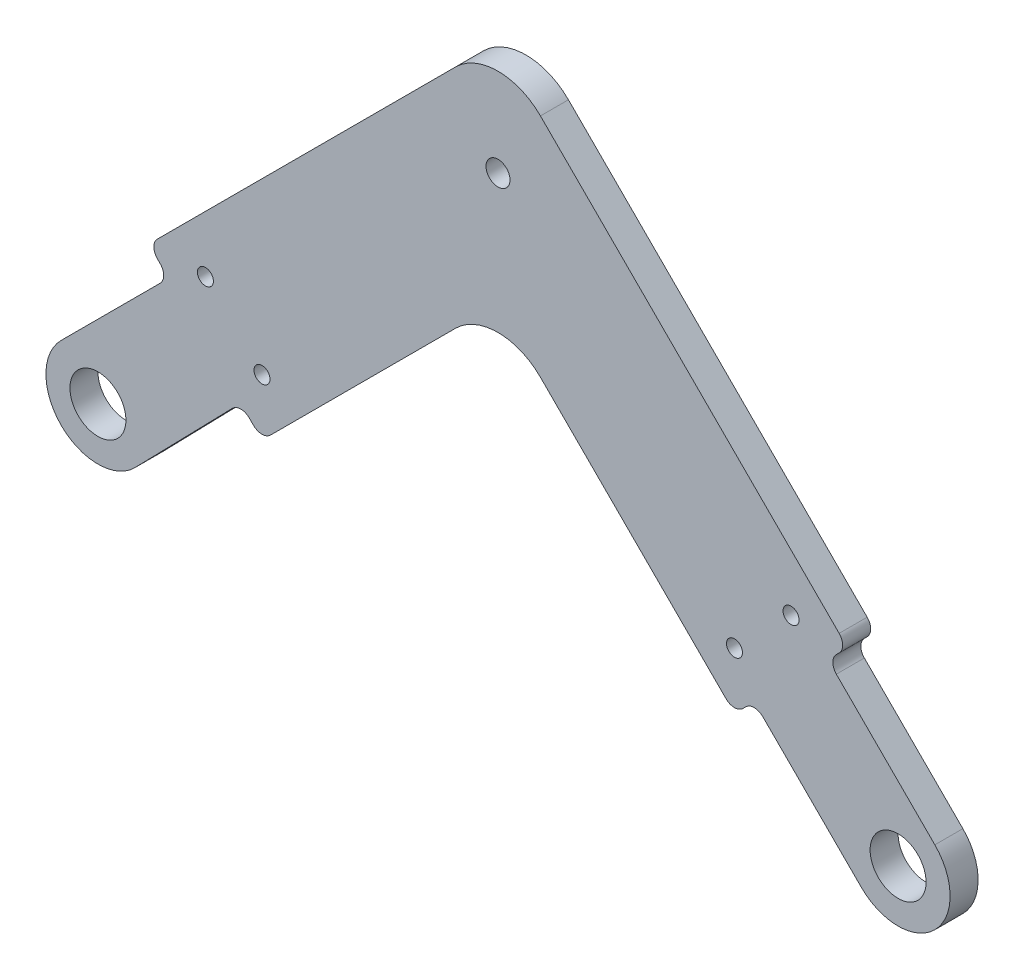
SolidWorks part; units mm, degrees
ref_plane "Front Plane" through (0, 0, 0) normal (0, 0, 1) x (1, 0, 0)
ref_plane "Top Plane" through (0, 0, 0) normal (0, 1, 0) x (1, 0, 0)
ref_plane "Right Plane" through (0, 0, 0) normal (1, 0, 0) x (0, 0, -1)
sketch "Sketch1" plane through (0, 0, 0) normal (0, 0, 1) x (1, 0, 0)
  line L0 (-100, 0) -> (100, 0) construction
  line L1 (0, 0) -> (0, 75.9094) construction
  line L2 (-40, 60) -> (40, 60) construction
  line L4 (0, 99.9354) -> (0, 75.9094) construction
  line L6 (0, 0) -> (-50, 50) construction
  line L7 (-100, 0) -> (0, 100) construction
  line L8 (0, 100) -> (100, 0) construction
  circle A0 centre (-100, 0) radius 20
  circle A1 centre (0, 0) radius 20
  circle A2 centre (100, 0) radius 20
  dimension "D4" = 40
  dimension "D1" = 200
  dimension "D2" = 100
  dimension "D3" = 80
sketch "Sketch3" plane through (0, 0, 0) normal (0, 0, 1) x (1, 0, 0)
  line L0 (-40, 60) -> (-56.5165, 43.4835) construction
  line L1 (81.9688, 8.8388) -> (95.4038, -4.5962)
  line L2 (-40, 60) -> (40, 60) construction
  line L3 (40, 60) -> (86.565, 13.435) construction
  line L4 (0, 100) -> (100, 0) construction
  line L5 (-100, 0) -> (0, 100) construction
  line L6 (44.1421, 70) -> (93.636, 20.5061)
  line L7 (-44.1421, 70) -> (44.1421, 70)
  line L8 (-44.1421, 70) -> (-63.5876, 50.5546)
  line L9 (35.8579, 50) -> (79.4939, 6.364)
  line L10 (-35.8579, 50) -> (35.8579, 50)
  line L11 (-35.8579, 50) -> (-49.4454, 36.4124)
  line L12 (-63.5876, 50.5546) -> (-49.4454, 36.4124)
  line L13 (79.4939, 6.364) -> (93.636, 20.5061)
  line L14 (104.5962, 4.5962) -> (91.1612, 18.0312)
  line L15 (0, 99.9354) -> (0, 75.9094) construction
  line L16 (-3.4532, 85.4203) -> (-6, 70)
  line L17 (3.4532, 85.4203) -> (6, 70)
  line L19 (0, 0) -> (0, 75.9094) construction
  line L20 (75.9584, 9.8995) -> (90.1005, 24.0416) construction
  circle A0 centre (100, 0) radius 10 construction
  circle A1 centre (100, 0) radius 3.5
  arc A2 (95.4038, -4.5962) -> (104.5962, 4.5962) centre (100, 0) ccw
  circle A3 centre (0, 60) radius 1.5
  circle A4 centre (0, 84.85) radius 1.5
  arc A5 (3.4532, 85.4203) -> (-3.4532, 85.4203) centre (0, 84.85) ccw
  circle A6 centre (79.4939, 13.435) radius 1
  circle A7 centre (86.565, 20.5061) radius 1
  circle A8 centre (0, 84.85) radius 3.5 construction
  circle A9 centre (100, 0) radius 6.5 construction
  circle A10 centre (-50, 50) radius 1.5
  dimension "D5" = 20
  dimension "D6" = 7
  dimension "D9" = 3
  dimension "D10" = 3
  dimension "D16" = 2
  dimension "D19" = 3
  dimension "D3" = 27.5
  dimension "D4" = 19
  dimension "D8" = 90
  dimension "D11" = 14.85
  dimension "D12" = 2
  dimension "D13" = 6
  dimension "D14" = 6
  dimension "D15" = 5
  dimension "D17" = 5
  dimension "D18" = 5
  dimension "D1" = 10
  dimension "D2" = 10
  dimension "D7" = 3
sketch "Sketch4" plane through (0, 0, 0) normal (0, 0, 1) x (1, 0, 0)
  line L0 (-86.565, 13.435) -> (-50, 50) construction
  line L1 (-100, 0) -> (0, 100) construction
  line L2 (-50, 50) -> (-13.3744, 13.3744) construction
  line L3 (0, 0) -> (-50, 50) construction
  line L4 (-79.4939, 6.364) -> (-50, 35.8579)
  line L5 (-50, 35.8579) -> (-20.4455, 6.3033)
  line L6 (-93.636, 20.5061) -> (-50, 64.1421)
  line L7 (-50, 64.1421) -> (-6.3033, 20.4455)
  line L8 (-93.636, 20.5061) -> (-79.4939, 6.364)
  line L10 (-82.1491, 9.0191) -> (-95.3424, -4.534)
  line L11 (-91.1612, 18.0312) -> (-104.5962, 4.5962)
  line L12 (-20.4455, 6.3033) -> (-6.3033, 20.4455)
  line L13 (-8.7782, 17.9706) -> (4.5962, 4.5962)
  line L14 (-17.9706, 8.7782) -> (-4.5962, -4.5962)
  line L15 (-90.1005, 24.0416) -> (-75.9584, 9.8995) construction
  line L16 (-23.981, 9.8389) -> (-9.8389, 23.981) construction
  circle A0 centre (-100, 0) radius 10 construction
  circle A1 centre (-100, 0) radius 3.5
  circle A2 centre (0, 0) radius 10 construction
  circle A3 centre (0, 0) radius 3.5
  circle A4 centre (100, 0) radius 10 construction
  arc A5 (-104.5962, 4.5962) -> (-95.3424, -4.534) centre (-100, 0) ccw
  circle A6 centre (100, 0) radius 3.5 construction
  arc A7 (-4.5962, -4.5962) -> (4.5962, 4.5962) centre (0, 0) ccw
  circle A8 centre (-100, 0) radius 20 construction
  circle A9 centre (-50, 50) radius 1.5 construction
  circle A10 centre (0, 0) radius 20 construction
  circle A11 centre (-100, 0) radius 6.5 construction
  circle A12 centre (0, 0) radius 6.5 construction
  circle A13 centre (-86.565, 20.5061) radius 1
  circle A14 centre (-79.4939, 13.435) radius 1
  circle A15 centre (-20.4455, 13.3744) radius 1
  circle A16 centre (-13.3744, 20.4455) radius 1
  circle A17 centre (-50, 50) radius 1.5
  dimension "D7" = 2
  dimension "D4" = 19
  dimension "D5" = 5
  dimension "D6" = 5
  dimension "D8" = 5
  dimension "D9" = 5
  dimension "D10" = 5
  dimension "D11" = 5
  dimension "D1" = 10
  dimension "D2" = 10
  dimension "D3" = 3
sketch "Sketch6" plane through (0, 0, 0) normal (0, 0, 1) x (1, 0, 0)
  line L0 (-57.5, 93.35) -> (57.5, 93.35)
  line L1 (57.5, 93.35) -> (57.5, 83.35)
  line L2 (57.5, 83.35) -> (44.1421, 70)
  line L3 (-57.5, 93.35) -> (-57.5, 83.35)
  line L4 (-57.5, 83.35) -> (-44.1421, 70)
  line L5 (-22.5, 84.85) -> (22.5, 84.85) construction
  line L6 (4, 60) -> (4, 70)
  line L7 (-44.1421, 70) -> (44.1421, 70) construction
  line L8 (-4, 60) -> (-4, 70)
  line L9 (-22.5, 89.35) -> (22.5, 89.35)
  line L12 (-22.5, 80.35) -> (22.5, 80.35)
  circle A0 centre (0, 60) radius 1.5 construction
  circle A1 centre (0, 60) radius 1.5
  circle A2 centre (0, 60) radius 4
  arc A5 (-22.5, 89.35) -> (-22.5, 80.35) centre (-22.5, 84.85) ccw
  arc A6 (22.5, 80.35) -> (22.5, 89.35) centre (22.5, 84.85) ccw
  point P8 (0, 93.35)
  point P23 (0, 84.85)
  dimension "D1" = 115
  dimension "D2" = 10
  dimension "D3" = 2.5
  dimension "D4" = 45
  dimension "D5" = 4
  dimension "D6" = 9
sketch "Sketch7" plane through (0, 0, 0) normal (0, 0, 1) x (1, 0, 0)
  line L0 (-91.1612, 18.0312) -> (-104.5962, 4.5962) construction
  line L1 (-82.1491, 9.0191) -> (-95.3424, -4.534) construction
  line L2 (-8.7782, 17.9706) -> (4.5962, 4.5962) construction
  line L3 (-17.9706, 8.7782) -> (-4.5962, -4.5962) construction
  line L4 (-91.1612, 18.0312) -> (-104.5962, 4.5962)
  line L5 (-82.1491, 9.0191) -> (-95.3424, -4.534)
  line L6 (-79.4939, 6.364) -> (-50, 35.8579)
  line L7 (-50, 35.8579) -> (-20.4455, 6.3033)
  line L8 (-20.4455, 6.3033) -> (-6.3033, 20.4455)
  line L9 (-6.3033, 20.4455) -> (-50, 64.1421)
  line L10 (-50, 64.1421) -> (-93.636, 20.5061)
  line L11 (-93.636, 20.5061) -> (-79.4939, 6.364)
  line L12 (-79.4939, 6.364) -> (-50, 35.8579)
  line L13 (-50, 35.8579) -> (-20.4455, 6.3033)
  line L14 (-20.4455, 6.3033) -> (-17.9706, 8.7782)
  line L15 (-6.3033, 20.4455) -> (-50, 64.1421)
  line L16 (-50, 64.1421) -> (-93.636, 20.5061)
  line L17 (-93.636, 20.5061) -> (-91.1612, 18.0312)
  line L18 (-8.7782, 17.9706) -> (4.5962, 4.5962)
  line L19 (-17.9706, 8.7782) -> (-4.5962, -4.5962)
  line L20 (-82.1491, 9.0191) -> (-79.4939, 6.364)
  line L21 (-8.7782, 17.9706) -> (-6.3033, 20.4455)
  arc A0 (-104.5962, 4.5962) -> (-95.3424, -4.534) centre (-100, 0) ccw construction
  circle A1 centre (0, 0) radius 3.5
  circle A2 centre (0, 0) radius 3.5
  circle A3 centre (-100, 0) radius 3.5
  circle A4 centre (-100, 0) radius 3.5
  circle A5 centre (-86.565, 20.5061) radius 1
  circle A6 centre (-86.565, 20.5061) radius 1
  circle A7 centre (-50, 50) radius 1.5
  circle A8 centre (-50, 50) radius 1.5
  circle A9 centre (-13.3744, 20.4455) radius 1
  circle A10 centre (-13.3744, 20.4455) radius 1
  circle A11 centre (-20.4455, 13.3744) radius 1
  circle A12 centre (-20.4455, 13.3744) radius 1
  circle A13 centre (-79.4939, 13.435) radius 1
  circle A14 centre (-79.4939, 13.435) radius 1
  arc A15 (-4.5962, -4.5962) -> (4.5962, 4.5962) centre (0, 0) ccw construction
  arc A16 (-104.5962, 4.5962) -> (-95.3424, -4.534) centre (-100, 0) ccw
  arc A17 (-4.5962, -4.5962) -> (4.5962, 4.5962) centre (0, 0) ccw
  dimension "D1" = 0
  dimension "D2" = 0
  dimension "D3" = 0
  dimension "D4" = 0
  dimension "D5" = 0
  dimension "D6" = 0
  dimension "D7" = 0
  dimension "D8" = 0
extrude "Boss-Extrude1" add sketch "Sketch7" along normal blind 3.5
fillet "Fillet1" radius 7.5 1 edges at (-50, 64.1421, 1.75)
fillet "Fillet2" radius 7.5 1 edges at (-50, 35.8579, 1.75)
fillet "Fillet3" radius 1.5 5 edges at (-93.636, 20.5061, 1.75) (-82.1491, 9.0191, 1.75) (-79.4939, 6.364, 1.75) (-17.9706, 8.7782, 1.75) (-20.4455, 6.3033, 1.75)
fillet "Fillet4" radius 1.5 2 edges at (-6.3033, 20.4455, 1.75) (-8.7782, 17.9706, 1.75)
fillet "Fillet5" radius 1.5 1 edges at (-91.1612, 18.0312, 1.75)
